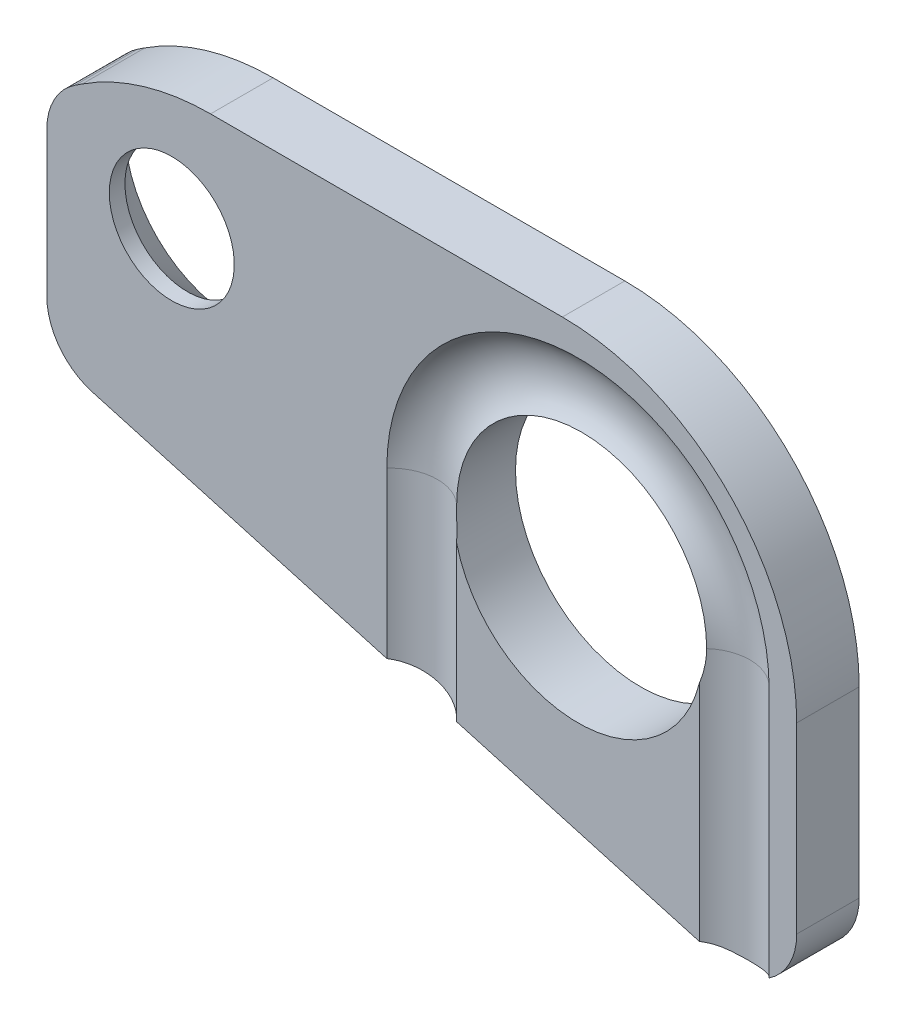
SolidWorks part; units mm, degrees
ref_plane "Front Plane" through (0, 0, 0) normal (0, 0, 1) x (1, 0, 0)
ref_plane "Top Plane" through (0, 0, 0) normal (0, 1, 0) x (1, 0, 0)
ref_plane "Right Plane" through (0, 0, 0) normal (1, 0, 0) x (0, 0, -1)
sketch "Sketch1" plane through (0, 0, 0) normal (0, 0, 1) x (1, 0, 0)
  line L5 (0, 0) -> (0, 34.5438) construction
  line L6 (-13, 8.9525) -> (-13, 4.3252)
  line L7 (-11.5462, 2.4012) -> (8.4538, -3.2771)
  line L8 (-11.8639, 10.7773) -> (-12.0945, 10.6265)
  line L9 (3.5, 12) -> (-7.7595, 12)
  line L10 (11, -1.3531) -> (11, 4.5)
  arc A7 (-13, 8.9525) -> (-12.0945, 10.6265) centre (-11, 8.9525) cw
  arc A8 (-11.5462, 2.4012) -> (-13, 4.3252) centre (-11, 4.3252) cw
  arc A9 (11, -1.3531) -> (8.4538, -3.2771) centre (9, -1.3531) cw
  arc A10 (-7.7595, 12) -> (-11.8639, 10.7773) centre (-7.7595, 4.5) ccw
  arc A11 (11, 4.5) -> (3.5, 12) centre (3.5, 4.5) ccw
  circle A12 centre (4, 5) radius 4
  circle A13 centre (-9, 8.2) radius 2
  point P0 (0, 0)
  point P11 (-11, 12)
  dimension "D1" = 4
  dimension "D2" = 5
extrude "Boss-Extrude1" add sketch "Sketch1" along normal blind 2
ref_plane "Plane1" through (0, 0, 3) normal (0, 0, 1) x (1, 0, 0)
sketch "Sketch19" plane through (0, 0, 3) normal (0, 0, 1) x (1, 0, 0)
  line L0 (-1, 5) -> (-1, -3.014)
  line L1 (9, 5) -> (9, -6.1349)
  arc A0 (9, 5) -> (-1, 5) centre (4, 5) ccw
  dimension "D1" = 10
sweep "Cut-Sweep2" cut path "Sketch19" circular profile diameter 3 parameters "D3"=3
chamfer "Chamfer1" distance 1.5 angle 45 1 edges at (-11, 8.2, 0)
